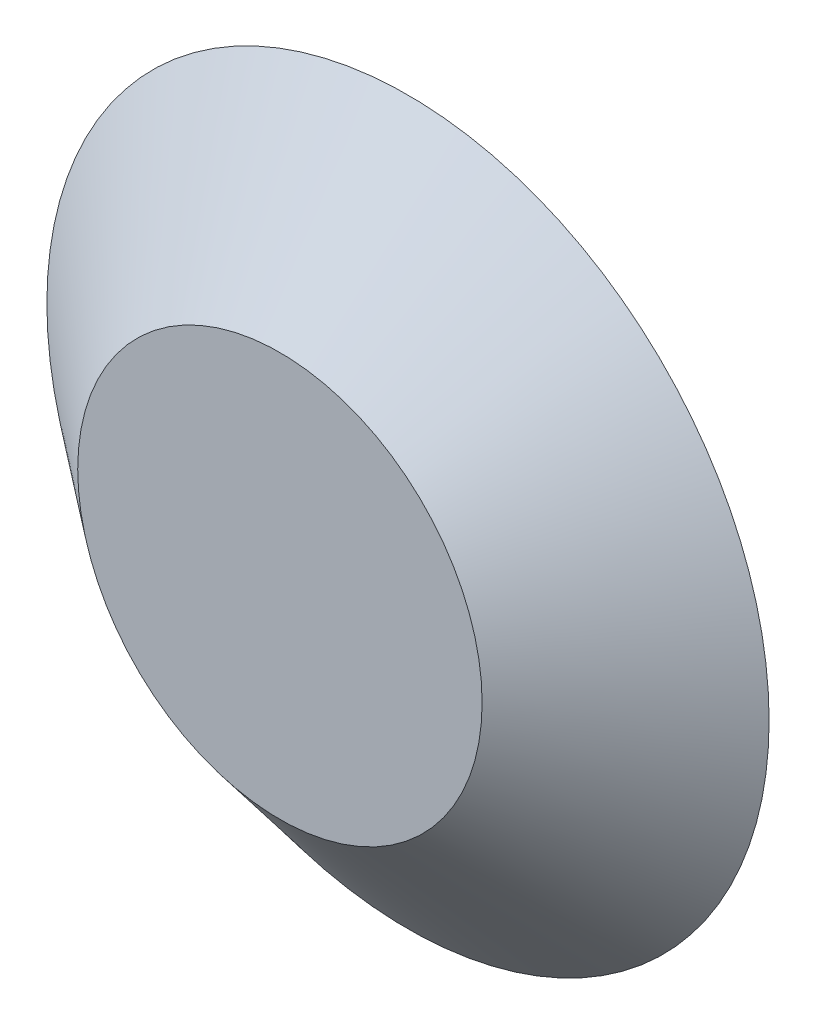
SolidWorks part; units mm, degrees
material "Bismuth"
ref_plane "Front" through (0, 0, 0) normal (0, 0, 1) x (1, 0, 0)
ref_plane "Top" through (0, 0, 0) normal (0, 1, 0) x (1, 0, 0)
ref_plane "Right" through (0, 0, 0) normal (1, 0, 0) x (0, 0, -1)
sketch "Sketch1" plane through (0, 0, 0) normal (0, 0, 1) x (1, 0, 0)
  circle A0 centre (0, 0) radius 128
extrude "Boss-Extrude1" add sketch "Sketch1" along normal blind 45.4 draft 51.13
